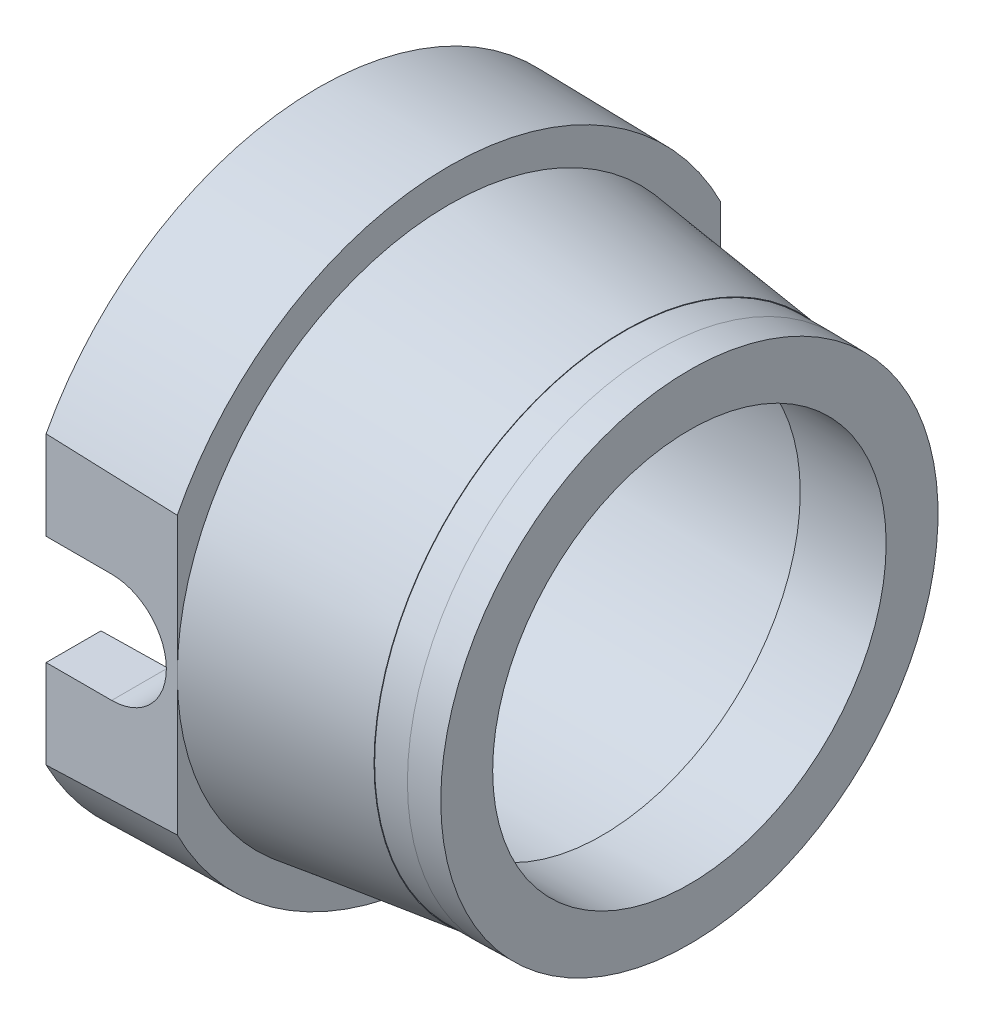
SolidWorks part; units mm, degrees
ref_plane "Front" through (0, 0, 0) normal (0, 0, 1) x (1, 0, 0)
ref_plane "Top" through (0, 0, 0) normal (0, 1, 0) x (1, 0, 0)
ref_plane "Right" through (0, 0, 0) normal (1, 0, 0) x (0, 0, -1)
sketch "草图1" plane through (0, 0, 0) normal (0, 0, 1) x (1, 0, 0)
  line L0 (-162.8045, 0) -> (7977.4181, 0) construction
  line L1 (0, -162.8045) -> (0, 7977.4181) construction
  line L2 (7, -5.7131) -> (8.5, -5.6869)
  line L3 (0, 0) -> (3, 0)
  line L4 (0, 0) -> (0, -7)
  line L5 (0, -7) -> (3, -7)
  line L6 (3, 0) -> (3, -7)
  line L7 (3, 0) -> (7, 0)
  line L8 (3, 0) -> (3, -6.5042)
  line L9 (3, -6.5042) -> (7, -6.5042)
  line L10 (7, 0) -> (7, -6.5042)
  line L11 (7, 0) -> (8.5, 0)
  line L12 (7, 0) -> (7, -5.7)
  line L13 (7, -5.7) -> (8.5, -5.7)
  line L14 (8.5, 0) -> (8.5, -5.7)
  line L15 (7, -5.7131) -> (3, -6.2134)
  line L16 (0, -7.0262) -> (3, -6.9738)
  line L17 (6.5, -4.5349) -> (8.5, -4.5)
  line L18 (8.5, 0) -> (6.5, 0)
  line L19 (8.5, 0) -> (8.5, -4.5)
  line L20 (8.5, -4.5) -> (6.5, -4.5)
  line L21 (6.5, 0) -> (6.5, -4.5)
  line L22 (6.5, -5) -> (6.5, -5.7756)
  line L23 (6.5, 0) -> (0, 0)
  line L24 (6.5, 0) -> (6.5, -5)
  line L25 (6.5, -5) -> (0, -5)
  line L26 (0, 0) -> (0, -5)
  line L27 (0, -5.1135) -> (6.5, -5)
  line L28 (0, -7) -> (0, -7.0262)
  line L29 (7, -5.7) -> (7, -5.7131)
  point P18 (7.75, -5.7)
  point P22 (1.5, -7)
  dimension "D1" = 7
  dimension "D2" = 5.7
  dimension "D3" = 3
  dimension "D4" = 1.5
  dimension "D5" = 8.5
  dimension "D6" = 1
  dimension "D7" = 7.13
  dimension "D8" = 2
  dimension "D9" = 4.5
  dimension "D10" = 5
revolve "旋转1" add sketch "草图1" angle 360 about L0
sketch "草图2" plane through (3, 0, 0) normal (1, 0, 0) x (0, 0, -1)
  line L1 (10.2274, 5.9503) -> (6.2134, 5.9503)
  line L2 (10.2274, 5.9503) -> (10.2274, -4.7659)
  line L3 (10.2274, -4.7659) -> (6.2134, -4.7659)
  line L4 (6.2134, 5.9503) -> (6.2134, -4.7659)
  line L5 (-9.3032, 5.9503) -> (-6.2134, 5.9503)
  line L6 (-9.3032, 5.9503) -> (-9.3032, -6.9127)
  line L7 (-9.3032, -6.9127) -> (-6.2134, -6.9127)
  line L8 (-6.2134, 5.9503) -> (-6.2134, -6.9127)
extrude "切除-拉伸1" cut sketch "草图2" against normal through all
sketch "草图3" plane through (0, 0, 6.2134) normal (0, 0, 1) x (1, 0, 0)
  line L0 (0, 3.2803) -> (0, -3.2803) construction
  line L1 (0, -1.25) -> (1.5, -1.25)
  line L2 (0, -1.25) -> (0, 1.25)
  line L3 (0, 1.25) -> (1.5, 1.25)
  line L4 (1.5, -1.25) -> (1.5, 1.25)
  circle A0 centre (1.5, 0) radius 1.25
  point P6 (0, 0)
  dimension "D4" = 2.5
  dimension "D1" = 0
  dimension "D2" = 2.5
  dimension "D3" = 1.5
extrude "切除-拉伸2" cut sketch "草图3" against normal up to next contours L3 L4 L1 L2 | A0
